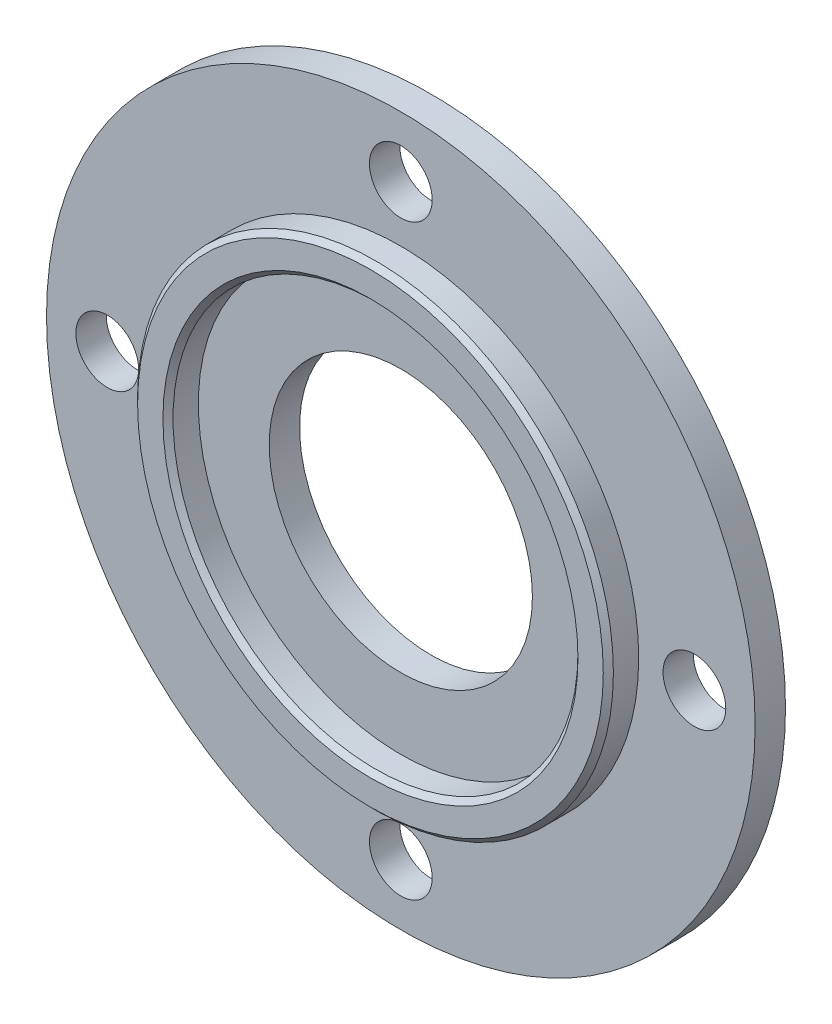
SolidWorks part; units mm, degrees
ref_plane "Front Plane" through (0, 0, 0) normal (0, 0, 1) x (1, 0, 0)
ref_plane "Top Plane" through (0, 0, 0) normal (0, 1, 0) x (1, 0, 0)
ref_plane "Right Plane" through (0, 0, 0) normal (1, 0, 0) x (0, 0, -1)
sketch "Sketch1" plane through (0, 0, 0) normal (0, 0, 1) x (1, 0, 0)
  circle A0 centre (0, 0) radius 35
  dimension "D1" = 70
extrude "Boss-Extrude1" add sketch "Sketch1" along normal blind 3
sketch "Sketch2" plane through (0, 0, 3) normal (0, 0, 1) x (1, 0, 0)
  circle A0 centre (0, 0) radius 13
  circle A1 centre (0, 0) radius 29
  circle A2 centre (29, 0) radius 3.1
  circle A3 centre (0, -29) radius 3.1
  circle A4 centre (-29, 0) radius 3.1
  circle A5 centre (0, 29) radius 3.1
  point P15 (0, 0)
  dimension "D1" = 26
  dimension "D2" = 58
  dimension "D3" = 6.2
  dimension "D4" = 4
extrude "Cut-Extrude1" cut sketch "Sketch2" against normal blind 3 contours A0 | A5 | A2 | A3 | A4
sketch "Sketch3" plane through (0, 0, 3) normal (0, 0, 1) x (1, 0, 0)
  circle A0 centre (0, 0) radius 23.5
  circle A1 centre (0, 0) radius 20
  dimension "D1" = 47
extrude "Boss-Extrude2" add sketch "Sketch3" along normal blind 3
chamfer "Chamfer1" distance 0.5 angle 45 1 edges at (23.5, 0, 6)
chamfer "Chamfer2" distance 0.5 angle 45 1 edges at (20, 0, 6)
